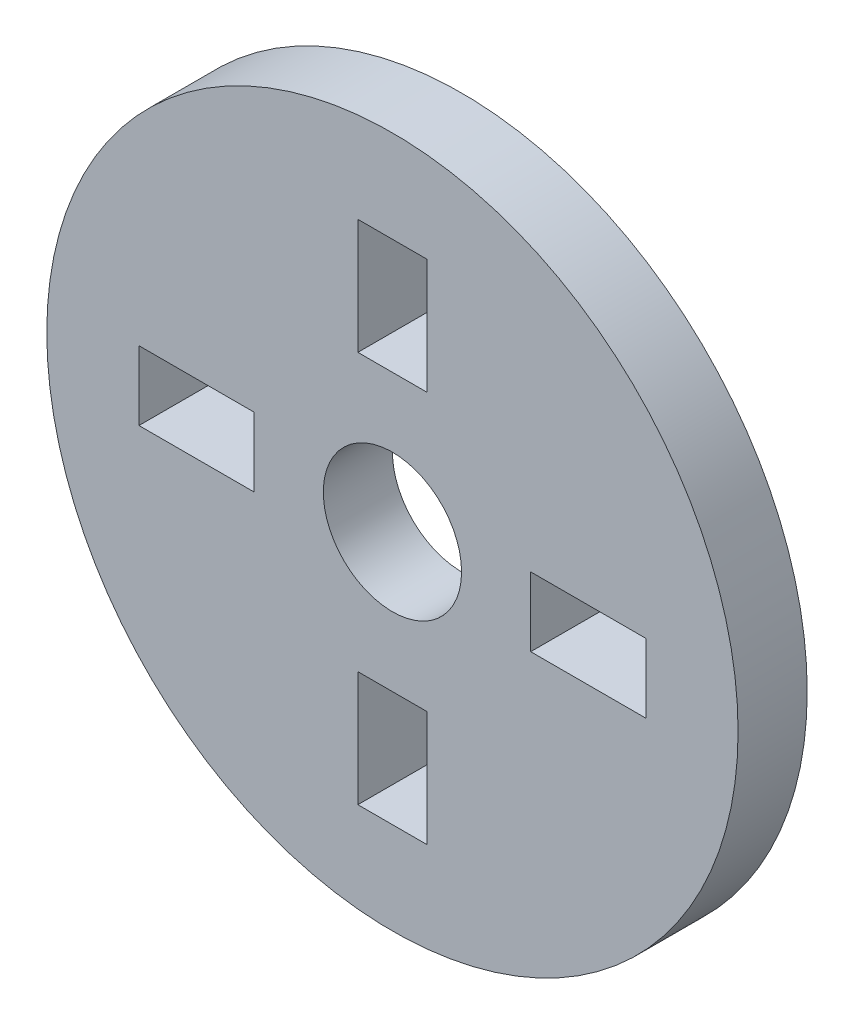
SolidWorks part; units mm, degrees
material "Cedar"
ref_plane "Front Plane" through (0, 0, 0) normal (0, 0, 1) x (1, 0, 0)
ref_plane "Top Plane" through (0, 0, 0) normal (0, 1, 0) x (1, 0, 0)
ref_plane "Right Plane" through (0, 0, 0) normal (1, 0, 0) x (0, 0, -1)
sketch "Sketch1" plane through (0, 0, 0) normal (0, 0, 1) x (1, 0, 0)
  circle A0 centre (0, 0) radius 3
  circle A1 centre (0, 0) radius 15
  dimension "D1" = 30
  dimension "D2" = 6
extrude "Boss-Extrude1" add sketch "Sketch1" along normal blind 3
sketch "Sketch2" plane through (0, 0, 3) normal (0, 0, 1) x (1, 0, 0)
  line L0 (6, 1.5) -> (11, 1.5)
  line L1 (-1.5, 6) -> (1.5, 6)
  line L2 (-1.5, 6) -> (-1.5, 11)
  line L3 (-1.5, 11) -> (1.5, 11)
  line L4 (1.5, 6) -> (1.5, 11)
  line L5 (-1.5, 6) -> (1.5, 11) construction
  line L6 (-1.5, 11) -> (1.5, 6) construction
  line L7 (6, 1.5) -> (6, -1.5)
  line L8 (6, -1.5) -> (11, -1.5)
  line L9 (11, 1.5) -> (11, -1.5)
  line L10 (1.5, -6) -> (1.5, -11)
  line L11 (1.5, -6) -> (-1.5, -6)
  line L12 (-1.5, -6) -> (-1.5, -11)
  line L13 (1.5, -11) -> (-1.5, -11)
  line L14 (-6, -1.5) -> (-11, -1.5)
  line L15 (-6, -1.5) -> (-6, 1.5)
  line L16 (-6, 1.5) -> (-11, 1.5)
  line L17 (-11, -1.5) -> (-11, 1.5)
  point P0 (0, 8.5)
  point P21 (0, 0)
  dimension "D1" = 6
  dimension "D2" = 3
  dimension "D3" = 0
  dimension "D4" = 5
  dimension "D5" = 4
extrude "Cut-Extrude1" cut sketch "Sketch2" against normal blind 3
